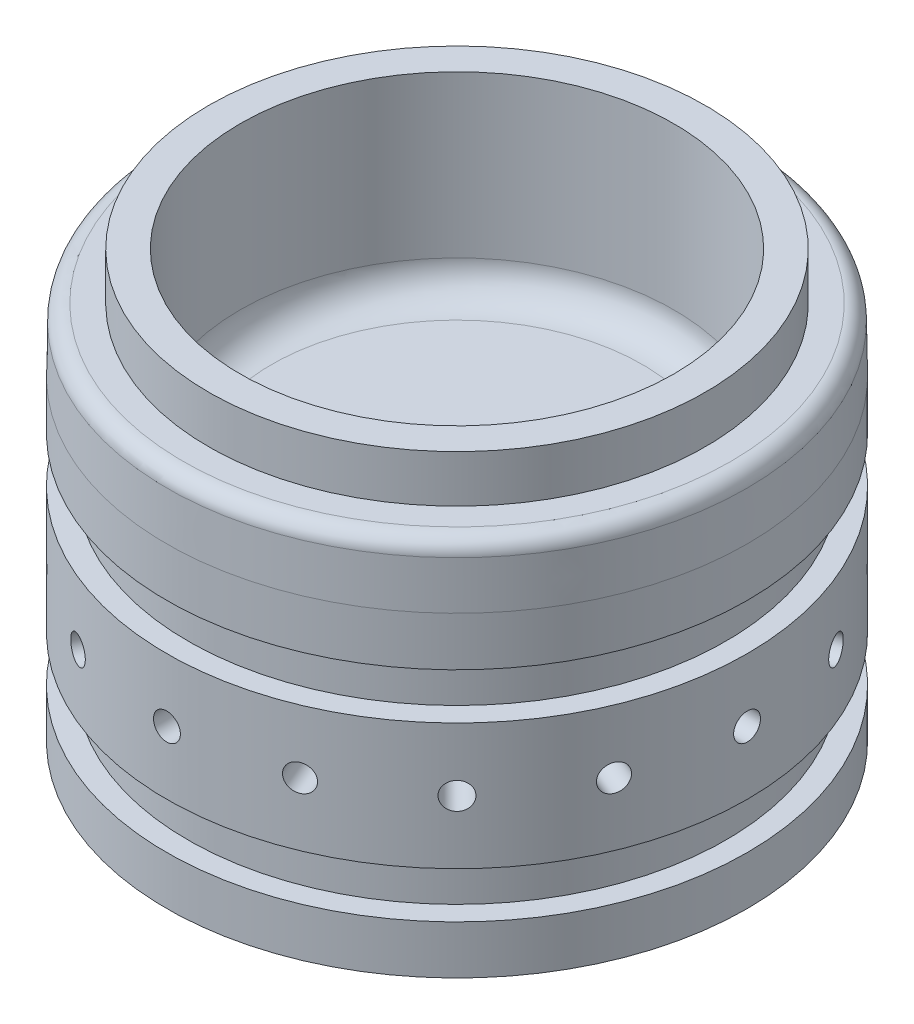
SolidWorks part; units mm, degrees
material "6061-T6 (SS)"
ref_plane "Front Plane" through (0, 0, 0) normal (0, 0, 1) x (1, 0, 0)
ref_plane "Top Plane" through (0, 0, 0) normal (0, 1, 0) x (1, 0, 0)
ref_plane "Right Plane" through (0, 0, 0) normal (1, 0, 0) x (0, 0, -1)
sketch "Sketch1" plane through (0, 0, 0) normal (0, 0, 1) x (1, 0, 0)
  line L11 (0, 0) -> (-58.4454, 0)
  line L14 (0, 0) -> (0, 15.24)
  line L16 (-43.6499, 15.24) -> (-43.6499, 54.0385)
  line L17 (0, 0) -> (0, -15.24)
  line L19 (-58.4454, -31.75) -> (-48.9331, -31.75)
  line L20 (-48.9331, -31.75) -> (-48.9331, -15.24)
  line L21 (-48.9331, -15.24) -> (0, -15.24)
  line L22 (0, 31.75) -> (0, -31.75) construction
  line L23 (-58.4454, 0) -> (-58.4454, 12.7)
  line L32 (-58.4454, 0) -> (-58.4454, -12.7)
  line L33 (-58.4454, 12.7) -> (-54.1274, 12.7)
  line L34 (-54.1274, 12.7) -> (-54.1274, 21.971)
  line L35 (-54.1274, 21.971) -> (-58.4454, 21.971)
  line L36 (-58.4454, 44.5262) -> (-58.4454, 21.971)
  line L37 (-58.4454, 44.5262) -> (-58.4454, 31.8262)
  line L38 (-58.4454, 31.8262) -> (-58.2364, 44.5262)
  line L39 (-58.4454, -12.7) -> (-54.1274, -12.7)
  line L40 (-58.4454, -21.971) -> (-58.4454, -31.75)
  line L41 (-49.9999, 54.0385) -> (-43.6499, 54.0385)
  line L42 (-58.4454, 44.5262) -> (-49.9999, 44.5262)
  line L43 (-49.9999, 44.5262) -> (-49.9999, 54.0385)
  line L44 (-43.6499, 15.24) -> (0, 15.24)
  line L45 (-54.1274, -12.7) -> (-54.1274, -21.971)
  line L46 (-54.1274, -21.971) -> (-58.4454, -21.971)
  dimension "D1" = 0
  dimension "D2" = 43.6499
  dimension "D3" = 48.9331
  dimension "D4" = 49.9999
  dimension "D5" = 54.1274
  dimension "D6" = 58.2364
  dimension "D7" = 58.4454
  dimension "D8" = 12.7
  dimension "D9" = 15.24
  dimension "D10" = 21.971
  dimension "D11" = 31.8262
  dimension "D12" = 31.75
revolve "Revolve1" add sketch "Sketch1" angle 360 about L22
ref_plane "HoleFacePlane" through (0, 0, -58.4454) normal (0, 0, -1) x (-1, 0, 0)
fillet "TaperFillet" radius 3.175 1 edges at (-58.2364, 44.5262, 0)
sketch "HoleReference" plane through (0, 0, -58.4454) normal (0, 0, -1) x (-1, 0, 0)
  line L0 (-58.4581, -31.75) -> (58.4581, -31.75) construction
  point P0 (0, 0)
  dimension "D1" = 31.75
hole_wizard "Tap Drill for 1/4-28 Tap1" positions "Sketch3" profile "Sketch4" hole size "1/4-28" standard "ANSI Inch"
sketch "Sketch3" plane through (0, 0, -58.4454) normal (0, 0, -1) x (-1, 0, 0)
  point P0 (0, 0)
sketch "Sketch4" plane through (0, 0, -58.4454) normal (1, 0, 0) x (0, 1, 0)
  line L0 (0, 0) -> (0, 20.6754)
  line L1 (0, 20.6754) -> (2.7051, 19.05)
  line L2 (2.7051, 19.05) -> (2.7051, 0)
  line L5 (2.7051, 0) -> (0, 0)
  line L10 (0, 20.6754) -> (-2.7051, 19.05) construction
  line L11 (0, -6.35) -> (0, 107.95) construction
  dimension "Hole Dia." = 5.4102
  dimension "Hole Depth" = 19.05
  dimension "Drill Angle" = 118
ref_axis "Centerline" through (0, -12.7, 0) along (0, 1, 0)
pattern_circular "HolePattern" count 16 over 360 about axis through (0, -12.7, 0) along (0, 1, 0) of "Tap Drill for 1/4-28 Tap1"
fillet "PocketFillets" radius 6.35 2 edges at (-43.6499, 15.24, 0) (-48.9331, -15.24, 0)
sketch "CNVAReference" plane through (0, 15.24, 0) normal (0, 1, 0) x (1, 0, 0)
  point P0 (0, 0)
sketch "InjectorReference" plane through (0, -15.24, 0) normal (0, -1, 0) x (1, 0, 0)
  point P0 (0, 0)
hole_wizard "Pipe Tap Drill for 1/2 Tap1" positions "Sketch7" profile "Sketch8" hole size "1/2" standard "ANSI Inch"
sketch "Sketch7" plane through (0, 15.24, 0) normal (0, 1, 0) x (1, 0, 0)
  point P0 (0, 0)
sketch "Sketch8" plane through (0, 15.24, 0) normal (1, 0, 0) x (0, 0, 1)
  line L0 (0, 0) -> (0, 52.3545)
  line L1 (0, 52.3545) -> (8.9281, 46.99)
  line L2 (8.9281, 46.99) -> (8.9281, 0)
  line L5 (8.9281, 0) -> (0, 0)
  line L10 (0, 52.3545) -> (-8.9281, 46.99) construction
  line L11 (0, -6.35) -> (0, 107.95) construction
  dimension "Hole Dia." = 17.8562
  dimension "Hole Depth" = 46.99
  dimension "Drill Angle" = 118
